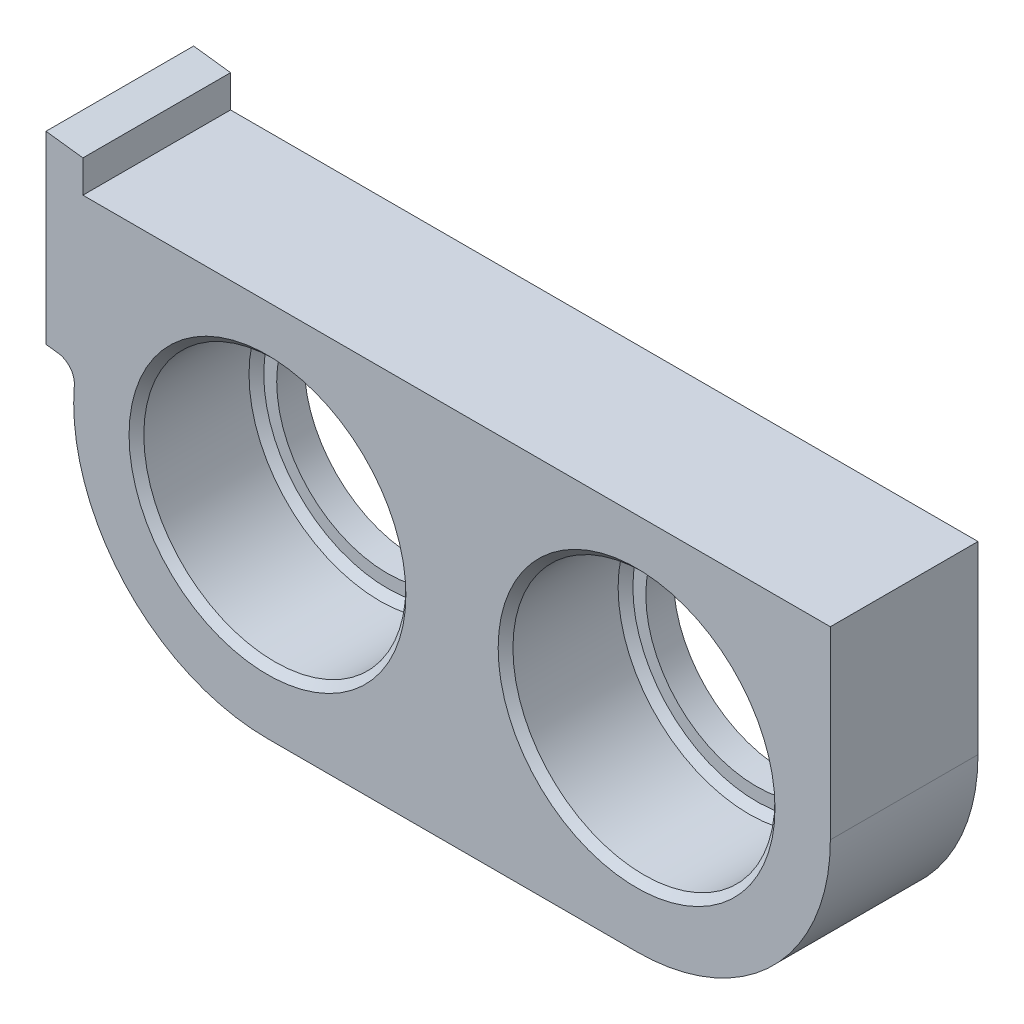
SolidWorks part; units mm, degrees
ref_plane "Front Plane" through (0, 0, 0) normal (0, 0, 1) x (1, 0, 0)
ref_plane "Top Plane" through (0, 0, 0) normal (0, 1, 0) x (1, 0, 0)
ref_plane "Right Plane" through (0, 0, 0) normal (1, 0, 0) x (0, 0, -1)
sketch "Sketch1" plane through (0, 0, 0) normal (0, 0, 1) x (1, 0, 0)
  line L0 (0, 0) -> (20, 0) construction
  line L1 (0, 10.5) -> (20, 10.5)
  line L2 (0, -10.5) -> (20, -10.5)
  line L3 (-12, 12) -> (0, 10.5)
  line L4 (-12, 12) -> (-12, 2)
  line L5 (-12, 2) -> (-10.3457, 1.7932)
  line L6 (20, 10.5) -> (30.5, 10.5)
  line L7 (30.5, 10.5) -> (30.5, 0)
  arc A0 (0, 10.5) -> (0, -10.5) centre (0, 0) ccw
  arc A1 (20, -10.5) -> (20, 10.5) centre (20, 0) ccw
  circle A2 centre (20, 0) radius 7.1
  circle A3 centre (0, 0) radius 7.1
  point P3 (10, 0)
  dimension "D2" = 10.5
  dimension "D3" = 14.2
  dimension "D1" = 20
  dimension "D4" = 10
  dimension "D5" = 12
  dimension "D6" = 12
extrude "Boss-Extrude1" add sketch "Sketch1" along normal blind 8
fillet "Fillet3" [suppressed] radius 100
sketch "Sketch2" plane through (0, 0, 0) normal (0, 0, -1) x (-1, 0, 0)
  circle A0 centre (0, 0) radius 6
  circle A1 centre (-20, 0) radius 7.1 construction
  circle A2 centre (0, 0) radius 7.1 construction
  circle A3 centre (-20, 0) radius 7.1
  circle A4 centre (0, 0) radius 7.1
  circle A5 centre (-20, 0) radius 6
  dimension "D1" = 12
extrude "Boss-Extrude2" add sketch "Sketch2" against normal blind 1.5
sketch "Sketch3" plane through (0, 0, 0) normal (1, 0, 0) x (0, 0, -1)
  line L0 (-4, 15) -> (-4, -17.1611) construction
  line L1 (0, -10.5) -> (0, 0) construction
  line L2 (-8, 0) -> (-8, -10.5) construction
  line L3 (-8, 10.5) -> (0, 10.5) construction
  line L5 (-9, 20) -> (1, 20)
  line L6 (-9, 20) -> (-9, 10)
  line L7 (-9, 10) -> (1, 10)
  line L8 (1, 20) -> (1, 10)
  line L9 (-9, 20) -> (1, 10) construction
  line L10 (-9, 10) -> (1, 20) construction
  circle A0 centre (-4, 15) radius 6.4
  dimension "D1" = 12.8
  dimension "D2" = 4.5
  dimension "D3" = 10
  dimension "D4" = 10
extrude "Cut-Extrude1" cut sketch "Sketch3" along normal through all and the other way blind 10 contours L6 L7 L8 L5
fillet "Fillet4" radius 1 1 edges at (-10.3457, 1.7932, 4)
chamfer "Chamfer1" distance 0.4 angle 45 4 edges at (27.1, 0, 8) (12.9, 0, 1.5) (7.1, 0, 8) (-7.1, 0, 1.5)
